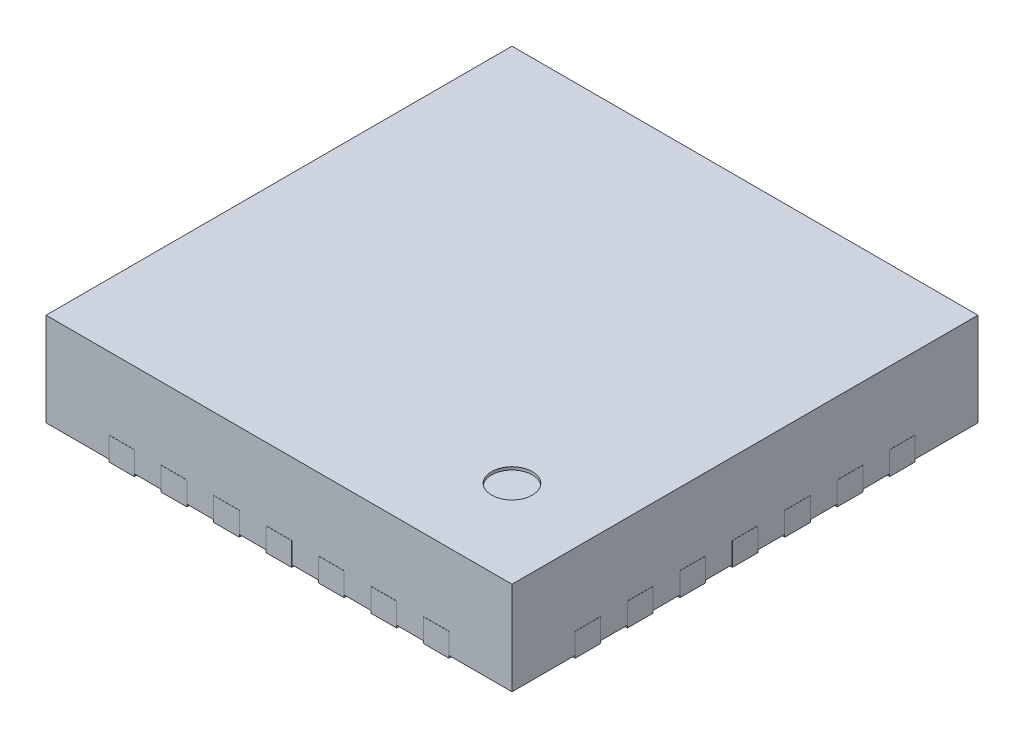
SolidWorks part; units mm, degrees
ref_plane "Front Plane" through (0, 0, 0) normal (0, 0, 1) x (1, 0, 0)
ref_plane "Top Plane" through (0, 0, 0) normal (0, 1, 0) x (1, 0, 0)
ref_plane "Right Plane" through (0, 0, 0) normal (1, 0, 0) x (0, 0, -1)
sketch "Sketch1" plane through (0, 0, 0) normal (0, 1, 0) x (1, 0, 0)
  line L1 (-2, -2) -> (2, -2)
  line L2 (-2, -2) -> (-2, 2)
  line L3 (-2, 2) -> (2, 2)
  line L4 (2, -2) -> (2, 2)
  line L5 (-2, -2) -> (2, 2) construction
  line L6 (-2, 2) -> (2, -2) construction
  point P0 (0, 0)
  dimension "D1" = 4
  dimension "D2" = 4
extrude "Boss-Extrude1" add sketch "Sketch1" along normal blind 0.8
sketch "Sketch2" plane through (0, 0.8, 0) normal (0, 1, 0) x (-1, 0, 0)
  line L0 (-2, 2) -> (-2, -2) construction
  line L1 (2, 2) -> (-2, 2) construction
  circle A0 centre (-1.25, 1.25) radius 0.175
  dimension "D1" = 0.75
  dimension "D2" = 0.75
extrude "Cut-Extrude1" cut sketch "Sketch2" against normal blind 0.025
sketch "Sketch3" plane through (0, 0, 0) normal (0, -1, 0) x (1, 0, 0)
  line L0 (1.2, 0.95) -> (1.2, 1)
  line L1 (-1, -1.2) -> (1, -1.2)
  line L2 (-1.2, -1) -> (-1.2, 1)
  line L3 (-1, 1.2) -> (1, 1.2)
  line L4 (1.2, -1) -> (1.2, 0.55)
  line L5 (-1.2, -1.2) -> (1.2, 1.2) construction
  line L6 (-1.2, 1.2) -> (1.2, -1.2) construction
  arc A0 (1, 1.2) -> (1.2, 1) centre (1, 1) cw
  arc A1 (1, -1.2) -> (1.2, -1) centre (1, -1) ccw
  arc A2 (-1, -1.2) -> (-1.2, -1) centre (-1, -1) cw
  arc A3 (-1.2, 1) -> (-1, 1.2) centre (-1, 1) cw
  arc A4 (1.2, 0.95) -> (1.2, 0.55) centre (1.2, 0.75) ccw
  point P0 (0, 0)
  dimension "D3" = 0.2
  dimension "D5" = 0.2
  dimension "D1" = 2.4
  dimension "D2" = 2.4
  dimension "D4" = 0.45
extrude "Boss-Extrude2" add sketch "Sketch3" along normal blind 0.01
sketch "Sketch4" plane through (0, 0, 0) normal (0, -1, 0) x (1, 0, 0)
  line L0 (-2, 2) -> (2, -2) construction
  line L1 (1, 1.2) -> (-1, 1.2) construction
  line L2 (1.46, 1.599) -> (1.261, 1.4)
  line L3 (-1.46, 2.001) -> (-1.24, 2.001)
  line L4 (-1.46, 2.001) -> (-1.46, 1.599)
  line L5 (-1.46, 1.599) -> (-1.261, 1.4)
  line L6 (-1.24, 2.001) -> (-1.24, 1.4647)
  line L7 (0, 2) -> (0, -2) construction
  line L8 (-2, 2) -> (2, 2) construction
  line L9 (2, -2) -> (-2, -2) construction
  line L10 (-1.01, 2.001) -> (-0.79, 2.001)
  line L11 (-1.01, 2.001) -> (-1.01, 1.4647)
  line L12 (-0.79, 2.001) -> (-0.79, 1.4647)
  line L13 (-0.56, 2.001) -> (-0.34, 2.001)
  line L14 (-0.56, 2.001) -> (-0.56, 1.4647)
  line L15 (-0.34, 2.001) -> (-0.34, 1.4647)
  line L16 (-0.11, 2.001) -> (0.11, 2.001)
  line L17 (-0.11, 2.001) -> (-0.11, 1.4647)
  line L18 (0.11, 2.001) -> (0.11, 1.4647)
  line L19 (0.34, 2.001) -> (0.56, 2.001)
  line L20 (0.34, 2.001) -> (0.34, 1.4647)
  line L21 (0.56, 2.001) -> (0.56, 1.4647)
  line L22 (0.79, 2.001) -> (1.01, 2.001)
  line L23 (0.79, 2.001) -> (0.79, 1.4647)
  line L24 (1.01, 2.001) -> (1.01, 1.4647)
  line L25 (1.46, 2.001) -> (1.46, 1.599)
  line L26 (1.46, 2.001) -> (1.24, 2.001)
  line L27 (1.24, 2.001) -> (1.24, 1.4647)
  line L28 (1.599, -1.46) -> (1.4, -1.261)
  line L29 (2.001, 1.46) -> (2.001, 1.24)
  line L30 (2.001, 1.46) -> (1.599, 1.46)
  line L31 (1.599, 1.46) -> (1.4, 1.261)
  line L32 (2.001, 1.24) -> (1.4647, 1.24)
  line L33 (2.001, 1.01) -> (2.001, 0.79)
  line L34 (2.001, 1.01) -> (1.4647, 1.01)
  line L35 (2.001, 0.79) -> (1.4647, 0.79)
  line L36 (2.001, 0.56) -> (2.001, 0.34)
  line L37 (2.001, 0.56) -> (1.4647, 0.56)
  line L38 (2.001, 0.34) -> (1.4647, 0.34)
  line L39 (2.001, 0.11) -> (2.001, -0.11)
  line L40 (2.001, 0.11) -> (1.4647, 0.11)
  line L41 (2.001, -0.11) -> (1.4647, -0.11)
  line L42 (2.001, -0.34) -> (2.001, -0.56)
  line L43 (2.001, -0.34) -> (1.4647, -0.34)
  line L44 (2.001, -0.56) -> (1.4647, -0.56)
  line L45 (2.001, -0.79) -> (2.001, -1.01)
  line L46 (2.001, -0.79) -> (1.4647, -0.79)
  line L47 (2.001, -1.01) -> (1.4647, -1.01)
  line L48 (2.001, -1.46) -> (1.599, -1.46)
  line L49 (2.001, -1.46) -> (2.001, -1.24)
  line L50 (2.001, -1.24) -> (1.4647, -1.24)
  line L51 (-1.46, -1.599) -> (-1.261, -1.4)
  line L52 (1.46, -2.001) -> (1.24, -2.001)
  line L53 (1.46, -2.001) -> (1.46, -1.599)
  line L54 (1.46, -1.599) -> (1.261, -1.4)
  line L55 (1.24, -2.001) -> (1.24, -1.4647)
  line L56 (1.01, -2.001) -> (0.79, -2.001)
  line L57 (1.01, -2.001) -> (1.01, -1.4647)
  line L58 (0.79, -2.001) -> (0.79, -1.4647)
  line L59 (0.56, -2.001) -> (0.34, -2.001)
  line L60 (0.56, -2.001) -> (0.56, -1.4647)
  line L61 (0.34, -2.001) -> (0.34, -1.4647)
  line L62 (0.11, -2.001) -> (-0.11, -2.001)
  line L63 (0.11, -2.001) -> (0.11, -1.4647)
  line L64 (-0.11, -2.001) -> (-0.11, -1.4647)
  line L65 (-0.34, -2.001) -> (-0.56, -2.001)
  line L66 (-0.34, -2.001) -> (-0.34, -1.4647)
  line L67 (-0.56, -2.001) -> (-0.56, -1.4647)
  line L68 (-0.79, -2.001) -> (-1.01, -2.001)
  line L69 (-0.79, -2.001) -> (-0.79, -1.4647)
  line L70 (-1.01, -2.001) -> (-1.01, -1.4647)
  line L71 (-1.46, -2.001) -> (-1.46, -1.599)
  line L72 (-1.46, -2.001) -> (-1.24, -2.001)
  line L73 (-1.24, -2.001) -> (-1.24, -1.4647)
  line L74 (-1.599, 1.46) -> (-1.4, 1.261)
  line L75 (-2.001, -1.46) -> (-2.001, -1.24)
  line L76 (-2.001, -1.46) -> (-1.599, -1.46)
  line L77 (-1.599, -1.46) -> (-1.4, -1.261)
  line L78 (-2.001, -1.24) -> (-1.4647, -1.24)
  line L79 (-2.001, -1.01) -> (-2.001, -0.79)
  line L80 (-2.001, -1.01) -> (-1.4647, -1.01)
  line L81 (-2.001, -0.79) -> (-1.4647, -0.79)
  line L82 (-2.001, -0.56) -> (-2.001, -0.34)
  line L83 (-2.001, -0.56) -> (-1.4647, -0.56)
  line L84 (-2.001, -0.34) -> (-1.4647, -0.34)
  line L85 (-2.001, -0.11) -> (-2.001, 0.11)
  line L86 (-2.001, -0.11) -> (-1.4647, -0.11)
  line L87 (-2.001, 0.11) -> (-1.4647, 0.11)
  line L88 (-2.001, 0.34) -> (-2.001, 0.56)
  line L89 (-2.001, 0.34) -> (-1.4647, 0.34)
  line L90 (-2.001, 0.56) -> (-1.4647, 0.56)
  line L91 (-2.001, 0.79) -> (-2.001, 1.01)
  line L92 (-2.001, 0.79) -> (-1.4647, 0.79)
  line L93 (-2.001, 1.01) -> (-1.4647, 1.01)
  line L94 (-2.001, 1.46) -> (-1.599, 1.46)
  line L95 (-2.001, 1.46) -> (-2.001, 1.24)
  line L96 (-2.001, 1.24) -> (-1.4647, 1.24)
  arc A0 (1.261, 1.4) -> (1.24, 1.4647) centre (1.35, 1.4647) cw
  arc A1 (-1.01, 1.4647) -> (-0.79, 1.4647) centre (-0.9, 1.4647) ccw
  arc A2 (-0.56, 1.4647) -> (-0.34, 1.4647) centre (-0.45, 1.4647) ccw
  arc A3 (-0.11, 1.4647) -> (0.11, 1.4647) centre (0, 1.4647) ccw
  arc A4 (0.34, 1.4647) -> (0.56, 1.4647) centre (0.45, 1.4647) ccw
  arc A5 (0.79, 1.4647) -> (1.01, 1.4647) centre (0.9, 1.4647) ccw
  arc A6 (-1.261, 1.4) -> (-1.24, 1.4647) centre (-1.35, 1.4647) ccw
  arc A7 (-1.46, 1.4647) -> (-1.4599, 1.4599) centre (-1.35, 1.4647) ccw [skipped]
  arc A8 (1.4, -1.261) -> (1.4647, -1.24) centre (1.4647, -1.35) cw
  arc A9 (1.4647, 1.01) -> (1.4647, 0.79) centre (1.4647, 0.9) ccw
  arc A10 (1.4647, 0.56) -> (1.4647, 0.34) centre (1.4647, 0.45) ccw
  arc A11 (1.4647, 0.11) -> (1.4647, -0.11) centre (1.4647, 0) ccw
  arc A12 (1.4647, -0.34) -> (1.4647, -0.56) centre (1.4647, -0.45) ccw
  arc A13 (1.4647, -0.79) -> (1.4647, -1.01) centre (1.4647, -0.9) ccw
  arc A14 (1.4, 1.261) -> (1.4647, 1.24) centre (1.4647, 1.35) ccw
  arc A15 (-1.261, -1.4) -> (-1.24, -1.4647) centre (-1.35, -1.4647) cw
  arc A16 (1.01, -1.4647) -> (0.79, -1.4647) centre (0.9, -1.4647) ccw
  arc A17 (0.56, -1.4647) -> (0.34, -1.4647) centre (0.45, -1.4647) ccw
  arc A18 (0.11, -1.4647) -> (-0.11, -1.4647) centre (0, -1.4647) ccw
  arc A19 (-0.34, -1.4647) -> (-0.56, -1.4647) centre (-0.45, -1.4647) ccw
  arc A20 (-0.79, -1.4647) -> (-1.01, -1.4647) centre (-0.9, -1.4647) ccw
  arc A21 (1.261, -1.4) -> (1.24, -1.4647) centre (1.35, -1.4647) ccw
  arc A22 (-1.4, 1.261) -> (-1.4647, 1.24) centre (-1.4647, 1.35) cw
  arc A23 (-1.4647, -1.01) -> (-1.4647, -0.79) centre (-1.4647, -0.9) ccw
  arc A24 (-1.4647, -0.56) -> (-1.4647, -0.34) centre (-1.4647, -0.45) ccw
  arc A25 (-1.4647, -0.11) -> (-1.4647, 0.11) centre (-1.4647, 0) ccw
  arc A26 (-1.4647, 0.34) -> (-1.4647, 0.56) centre (-1.4647, 0.45) ccw
  arc A27 (-1.4647, 0.79) -> (-1.4647, 1.01) centre (-1.4647, 0.9) ccw
  arc A28 (-1.4, -1.261) -> (-1.4647, -1.24) centre (-1.4647, -1.35) ccw
  point P10 (-1.35, 2.001)
  dimension "D7" = 0.11
  dimension "D2" = 0.22
  dimension "D3" = 1.35
  dimension "D4" = 0.001
  dimension "D1" = 6
  dimension "D5" = 0.2
  dimension "D6" = 4
extrude "Boss-Extrude3" add sketch "Sketch4" along normal blind 0.02 and the other way blind 0.18
